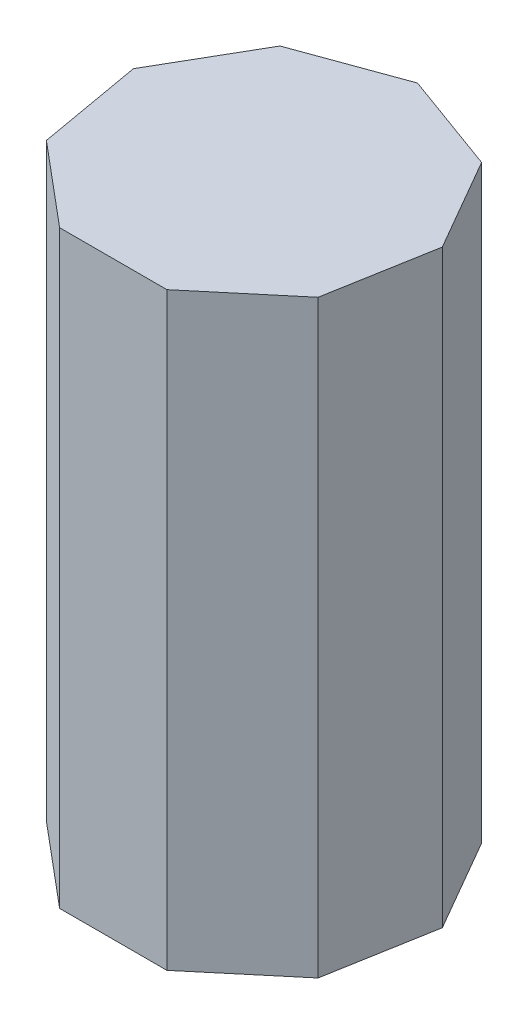
SolidWorks part; units mm, degrees
ref_plane "Front" through (0, 0, 0) normal (0, 0, 1) x (1, 0, 0)
ref_plane "Top" through (0, 0, 0) normal (0, 1, 0) x (1, 0, 0)
ref_plane "Right" through (0, 0, 0) normal (1, 0, 0) x (0, 0, -1)
sketch "Sketch1" plane through (0, 0, 0) normal (0, 1, 0) x (1, 0, 0)
  line L1 (5.2401, 0.924) -> (3.4202, 4.076)
  line L2 (3.4202, 4.076) -> (0, 5.3209)
  line L3 (0, 5.3209) -> (-3.4202, 4.076)
  line L4 (-3.4202, 4.076) -> (-5.2401, 0.924)
  line L5 (-5.2401, 0.924) -> (-4.608, -2.6604)
  line L6 (-4.608, -2.6604) -> (-1.8199, -5)
  line L7 (-1.8199, -5) -> (1.8199, -5)
  line L8 (1.8199, -5) -> (4.608, -2.6604)
  line L9 (4.608, -2.6604) -> (5.2401, 0.924)
  circle A0 centre (0, 0) radius 5 construction
  dimension "D1" = 10
extrude "Extrude1" add sketch "Sketch1" along normal blind 20
